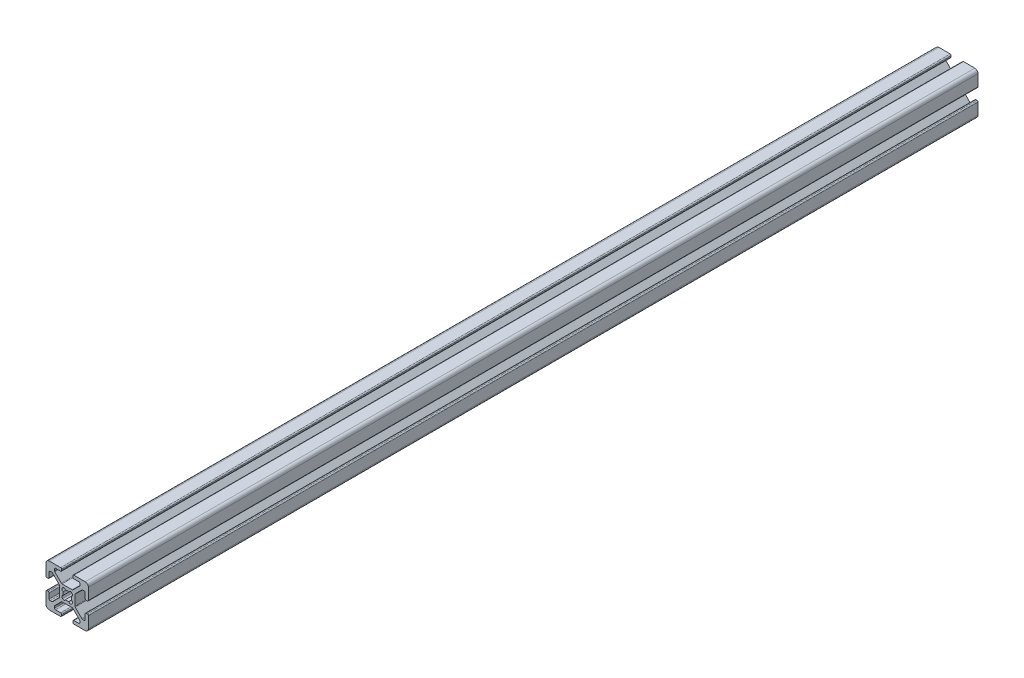
SolidWorks part; units mm, degrees
material "6105-T5 Aluminum"
ref_plane "Front Plane" through (0, 0, 0) normal (0, 0, 1) x (1, 0, 0)
ref_plane "Top Plane" through (0, 0, 0) normal (0, 1, 0) x (1, 0, 0)
ref_plane "Right Plane" through (0, 0, 0) normal (1, 0, 0) x (0, 0, -1)
sketch "Sketch1" plane through (0, 0, 0) normal (0, 0, 1) x (1, 0, 0)
  line L0 (9.492, 2.63) -> (9.008, 2.63)
  line L1 (8.5, 3.138) -> (8.5, 5.487)
  line L2 (10, 3.138) -> (10, 8.5)
  line L3 (3.655, -2.3839) -> (3.655, 2.3839)
  line L4 (7.2661, 5.995) -> (7.992, 5.995)
  line L5 (6.9069, 5.8462) -> (3.8038, 2.7431)
  line L6 (9.492, -2.63) -> (9.008, -2.63)
  line L7 (10, -3.138) -> (10, -8.5)
  line L8 (8.5, -3.138) -> (8.5, -5.487)
  line L9 (7.2661, -5.995) -> (7.992, -5.995)
  line L10 (6.9069, -5.8462) -> (3.8038, -2.7431)
  line L11 (2.1249, -2.3045) -> (2.3045, -2.1249)
  line L12 (-2.63, 9.492) -> (-2.63, 9.008)
  line L13 (-3.138, 10) -> (-8.5, 10)
  line L14 (-3.138, 8.5) -> (-5.487, 8.5)
  line L15 (2.3839, 3.655) -> (-2.3839, 3.655)
  line L16 (-5.995, 7.2661) -> (-5.995, 7.992)
  line L17 (-5.8462, 6.9069) -> (-2.7431, 3.8038)
  line L18 (2.63, 9.492) -> (2.63, 9.008)
  line L19 (3.138, 10) -> (8.5, 10)
  line L20 (3.138, 8.5) -> (5.487, 8.5)
  line L21 (5.995, 7.2661) -> (5.995, 7.992)
  line L22 (5.8462, 6.9069) -> (2.7431, 3.8038)
  line L23 (2.3045, 2.1249) -> (2.1249, 2.3045)
  line L24 (-9.492, -2.63) -> (-9.008, -2.63)
  line L25 (-10, -3.138) -> (-10, -8.5)
  line L26 (-8.5, -3.138) -> (-8.5, -5.487)
  line L27 (-3.655, 2.3839) -> (-3.655, -2.3839)
  line L28 (-7.2661, -5.995) -> (-7.992, -5.995)
  line L29 (-6.9069, -5.8462) -> (-3.8038, -2.7431)
  line L30 (-9.492, 2.63) -> (-9.008, 2.63)
  line L31 (-10, 3.138) -> (-10, 8.5)
  line L32 (-8.5, 3.138) -> (-8.5, 5.487)
  line L33 (-7.2661, 5.995) -> (-7.992, 5.995)
  line L34 (-6.9069, 5.8462) -> (-3.8038, 2.7431)
  line L35 (-2.1249, 2.3045) -> (-2.3045, 2.1249)
  line L36 (2.63, -9.492) -> (2.63, -9.008)
  line L37 (3.138, -10) -> (8.5, -10)
  line L38 (3.138, -8.5) -> (5.487, -8.5)
  line L39 (-2.3839, -3.655) -> (2.3839, -3.655)
  line L40 (5.995, -7.2661) -> (5.995, -7.992)
  line L41 (5.8462, -6.9069) -> (2.7431, -3.8038)
  line L42 (-2.63, -9.492) -> (-2.63, -9.008)
  line L43 (-3.138, -10) -> (-8.5, -10)
  line L44 (-3.138, -8.5) -> (-5.487, -8.5)
  line L45 (-5.995, -7.2661) -> (-5.995, -7.992)
  line L46 (-5.8462, -6.9069) -> (-2.7431, -3.8038)
  line L47 (-2.3045, -2.1249) -> (-2.1249, -2.3045)
  arc A0 (-0.804, -1.9351) -> (0.804, -1.9351) centre (0, 0) ccw
  arc A1 (8.5, 5.487) -> (7.992, 5.995) centre (7.992, 5.487) ccw
  arc A2 (7.2661, 5.995) -> (6.9069, 5.8462) centre (7.2661, 5.487) ccw
  arc A3 (3.8038, 2.7431) -> (3.655, 2.3839) centre (4.163, 2.3839) ccw
  arc A4 (3.655, -2.3839) -> (3.8038, -2.7431) centre (4.163, -2.3839) ccw
  arc A5 (6.9069, -5.8462) -> (7.2661, -5.995) centre (7.2661, -5.487) ccw
  arc A6 (7.992, -5.995) -> (8.5, -5.487) centre (7.992, -5.487) ccw
  arc A7 (9.008, -2.63) -> (8.5, -3.138) centre (9.008, -3.138) ccw
  arc A8 (10, -3.138) -> (9.492, -2.63) centre (9.492, -3.138) ccw
  arc A9 (9.492, 2.63) -> (10, 3.138) centre (9.492, 3.138) ccw
  arc A10 (8.5, 3.138) -> (9.008, 2.63) centre (9.008, 3.138) ccw
  arc A11 (0.804, -1.9351) -> (2.1249, -2.3045) centre (1.5684, -1.748) ccw
  arc A12 (2.3045, -2.1249) -> (1.9351, -0.804) centre (1.748, -1.5684) ccw
  arc A13 (-2.63, 9.492) -> (-3.138, 10) centre (-3.138, 9.492) ccw
  arc A14 (-3.138, 8.5) -> (-2.63, 9.008) centre (-3.138, 9.008) ccw
  arc A15 (1.9351, -0.804) -> (1.9351, 0.804) centre (0, 0) ccw
  arc A16 (-2.7431, 3.8038) -> (-2.3839, 3.655) centre (-2.3839, 4.163) ccw
  arc A17 (-5.487, 8.5) -> (-5.995, 7.992) centre (-5.487, 7.992) ccw
  arc A18 (-5.995, 7.2661) -> (-5.8462, 6.9069) centre (-5.487, 7.2661) ccw
  arc A19 (2.63, 9.008) -> (3.138, 8.5) centre (3.138, 9.008) ccw
  arc A20 (3.138, 10) -> (2.63, 9.492) centre (3.138, 9.492) ccw
  arc A21 (5.995, 7.992) -> (5.487, 8.5) centre (5.487, 7.992) ccw
  arc A22 (5.8462, 6.9069) -> (5.995, 7.2661) centre (5.487, 7.2661) ccw
  arc A23 (2.3839, 3.655) -> (2.7431, 3.8038) centre (2.3839, 4.163) ccw
  arc A24 (1.9351, 0.804) -> (2.3045, 2.1249) centre (1.748, 1.5684) ccw
  arc A25 (2.1249, 2.3045) -> (0.804, 1.9351) centre (1.5684, 1.748) ccw
  arc A26 (-9.492, -2.63) -> (-10, -3.138) centre (-9.492, -3.138) ccw
  arc A27 (-8.5, -3.138) -> (-9.008, -2.63) centre (-9.008, -3.138) ccw
  arc A28 (0.804, 1.9351) -> (-0.804, 1.9351) centre (0, 0) ccw
  arc A29 (-3.8038, -2.7431) -> (-3.655, -2.3839) centre (-4.163, -2.3839) ccw
  arc A30 (-8.5, -5.487) -> (-7.992, -5.995) centre (-7.992, -5.487) ccw
  arc A31 (-7.2661, -5.995) -> (-6.9069, -5.8462) centre (-7.2661, -5.487) ccw
  arc A32 (-9.008, 2.63) -> (-8.5, 3.138) centre (-9.008, 3.138) ccw
  arc A33 (-10, 3.138) -> (-9.492, 2.63) centre (-9.492, 3.138) ccw
  arc A34 (-7.992, 5.995) -> (-8.5, 5.487) centre (-7.992, 5.487) ccw
  arc A35 (-6.9069, 5.8462) -> (-7.2661, 5.995) centre (-7.2661, 5.487) ccw
  arc A36 (-3.655, 2.3839) -> (-3.8038, 2.7431) centre (-4.163, 2.3839) ccw
  arc A37 (-0.804, 1.9351) -> (-2.1249, 2.3045) centre (-1.5684, 1.748) ccw
  arc A38 (-2.3045, 2.1249) -> (-1.9351, 0.804) centre (-1.748, 1.5684) ccw
  arc A39 (2.63, -9.492) -> (3.138, -10) centre (3.138, -9.492) ccw
  arc A40 (3.138, -8.5) -> (2.63, -9.008) centre (3.138, -9.008) ccw
  arc A41 (-1.9351, 0.804) -> (-1.9351, -0.804) centre (0, 0) ccw
  arc A42 (2.7431, -3.8038) -> (2.3839, -3.655) centre (2.3839, -4.163) ccw
  arc A43 (5.487, -8.5) -> (5.995, -7.992) centre (5.487, -7.992) ccw
  arc A44 (5.995, -7.2661) -> (5.8462, -6.9069) centre (5.487, -7.2661) ccw
  arc A45 (-2.63, -9.008) -> (-3.138, -8.5) centre (-3.138, -9.008) ccw
  arc A46 (-3.138, -10) -> (-2.63, -9.492) centre (-3.138, -9.492) ccw
  arc A47 (-5.995, -7.992) -> (-5.487, -8.5) centre (-5.487, -7.992) ccw
  arc A48 (-5.8462, -6.9069) -> (-5.995, -7.2661) centre (-5.487, -7.2661) ccw
  arc A49 (-2.3839, -3.655) -> (-2.7431, -3.8038) centre (-2.3839, -4.163) ccw
  arc A50 (-1.9351, -0.804) -> (-2.3045, -2.1249) centre (-1.748, -1.5684) ccw
  arc A51 (-2.1249, -2.3045) -> (-0.804, -1.9351) centre (-1.5684, -1.748) ccw
  arc A52 (10, 8.5) -> (8.5, 10) centre (8.5, 8.5) ccw
  arc A53 (8.5, -10) -> (10, -8.5) centre (8.5, -8.5) ccw
  arc A54 (-10, -8.5) -> (-8.5, -10) centre (-8.5, -8.5) ccw
  arc A55 (-8.5, 10) -> (-10, 8.5) centre (-8.5, 8.5) ccw
extrude "Extrude1" add sketch "Sketch1" against normal blind 420
